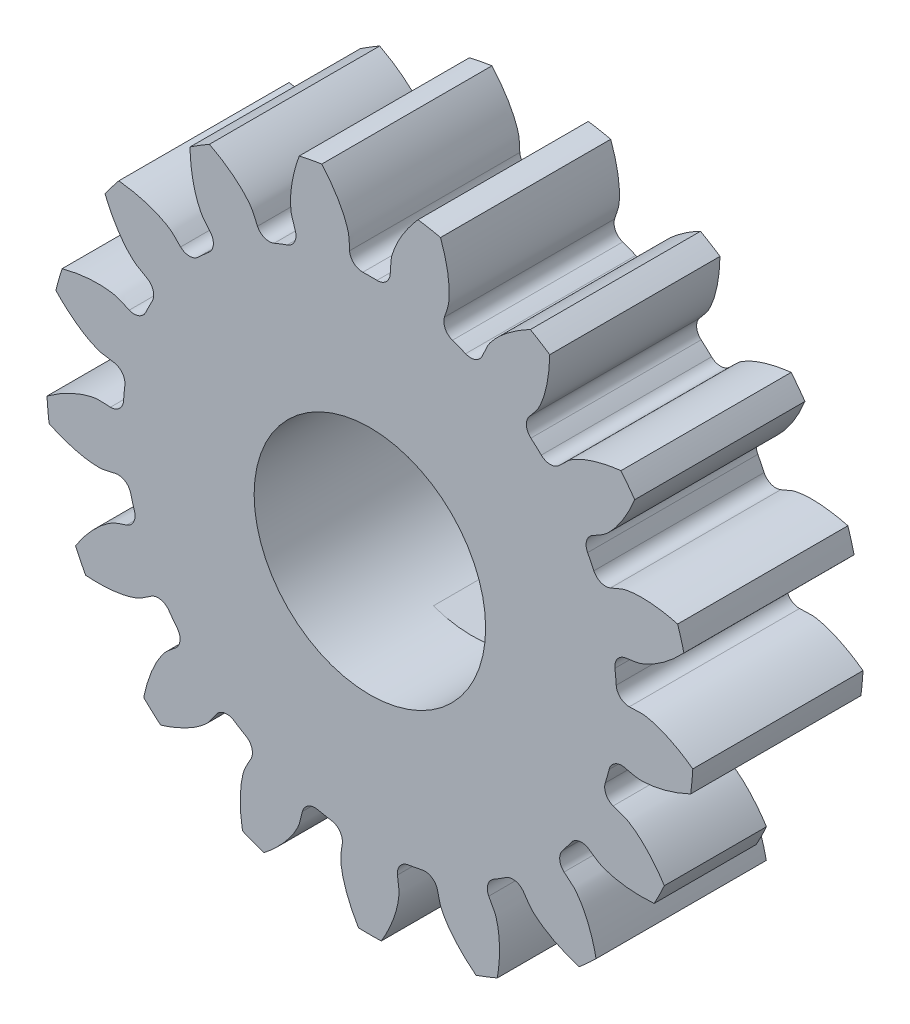
SolidWorks part; units mm, degrees
material "POM 乙缩醛共聚物"
ref_plane "前视基准面" through (0, 0, 0) normal (0, 0, 1) x (1, 0, 0)
ref_plane "上视基准面" through (0, 0, 0) normal (0, 1, 0) x (1, 0, 0)
ref_plane "右视基准面" through (0, 0, 0) normal (1, 0, 0) x (0, 0, -1)
ref_axis "Axis1" through (0, 0, -88.99) along (0, 0, 1)
sketch "草图1" plane through (0, 0, 0) normal (0, 0, 1) x (1, 0, 0)
  circle A0 centre (0, 0) radius 9.5
extrude "LaShenA" add sketch "草图1" along normal blind 5
sketch "SketchA" plane through (0, 0, 5) normal (0, 0, 1) x (1, 0, 0)
  line L0 (0, 0) -> (0, 9.5) construction
  arc A0 (0.207, 7.247) -> (-0.207, 7.247) centre (0, 0) ccw
  arc A1 (1.9284, 9.9057) -> (-1.9284, 9.9057) centre (0, 0) ccw
  arc A2 (-0.207, 7.247) -> (-0.5968, 7.5982) centre (-0.2179, 7.6269) cw
  arc A3 (0.5968, 7.5982) -> (0.207, 7.247) centre (0.2179, 7.6269) cw
  circle A4 centre (0, 0) radius 7.9874 construction
  circle A5 centre (0, 0) radius 9.5 construction
  circle A6 centre (0, 0) radius 7.25 construction
  circle A7 centre (0, 0) radius 8.5 construction
  spline S0 degree 3 poles (0.5968, 7.5982) (0.606, 7.7206) (0.6026, 7.8698) (0.6296, 8.029) (0.6422, 8.0808) (0.6533, 8.1218) (0.6675, 8.1687) (0.685, 8.2214) (0.7063, 8.2797) (0.7317, 8.3435) (0.7614, 8.4125) (0.7959, 8.4865) (0.8354, 8.5654) (0.8802, 8.6489) (0.9307, 8.7367) (0.987, 8.8286) (1.0495, 8.9244) (1.1185, 9.0236) (1.1941, 9.1262) (1.2767, 9.2316) (1.3664, 9.3397) (1.4635, 9.4501) (1.5682, 9.5624) (1.7212, 9.7175) (1.8433, 9.8309) (1.9284, 9.9057) knots 0.121184 0.121184 0.121184 0.121184 0.238206 0.264317 0.275812 0.289397 0.305072 0.322837 0.342692 0.364637 0.388672 0.414798 0.443013 0.473318 0.505713 0.540198 0.576773 0.615438 0.656194 0.699039 0.743974 0.790999 0.840114 0.89132 1 1 1 1
  spline S1 degree 3 poles (-0.5968, 7.5982) (-0.606, 7.7206) (-0.6026, 7.8698) (-0.6296, 8.029) (-0.6422, 8.0808) (-0.6533, 8.1218) (-0.6675, 8.1687) (-0.685, 8.2214) (-0.7063, 8.2797) (-0.7317, 8.3435) (-0.7614, 8.4125) (-0.7959, 8.4865) (-0.8354, 8.5654) (-0.8802, 8.6489) (-0.9307, 8.7367) (-0.987, 8.8286) (-1.0495, 8.9244) (-1.1185, 9.0236) (-1.1941, 9.1262) (-1.2767, 9.2316) (-1.3664, 9.3397) (-1.4635, 9.4501) (-1.5682, 9.5624) (-1.7212, 9.7175) (-1.8433, 9.8309) (-1.9284, 9.9057) knots 0.121184 0.121184 0.121184 0.121184 0.238206 0.264317 0.275812 0.289397 0.305072 0.322837 0.342692 0.364637 0.388672 0.414798 0.443013 0.473318 0.505713 0.540198 0.576773 0.615438 0.656194 0.699039 0.743974 0.790999 0.840114 0.89132 1 1 1 1
  dimension "D1" = 0.38
  dimension "Db" = 15.9748
  dimension "Da" = 19
  dimension "Df" = 14.5
  dimension "Dn" = 17
extrude "Cut-ExtrudeA" cut sketch "SketchA" against normal blind 30
pattern_circular "www.KYTool.cn" count 17 over 360 about axis through (0, 0, -88.99) along (0, 0, 1) of "Cut-ExtrudeA"
sketch "草图3" plane through (0, 0, 0) normal (0, 0, -1) x (-1, 0, 0)
  line L2 (-13.5943, -8.4259) -> (1.1359, -3.2046)
  line L3 (-1.7247, 2.9301) -> (-15.1929, -4.9977)
  line L4 (-13.5943, -8.4259) -> (1.1359, -3.2046)
  line L5 (-1.7247, 2.9301) -> (-15.1929, -4.9977)
  arc A2 (1.1359, -3.2046) -> (-1.7247, 2.9301) centre (0, 0) ccw
  arc A3 (-15.1929, -4.9977) -> (-13.5943, -8.4259) centre (-14.229, -6.6351) ccw
  arc A4 (1.1359, -3.2046) -> (-1.7247, 2.9301) centre (0, 0) ccw
  arc A5 (-15.1929, -4.9977) -> (-13.5943, -8.4259) centre (-14.229, -6.6351) ccw
  dimension "D1" = 0
extrude "切除-拉伸2" cut sketch "草图3" against normal up to surface (2 mm away)
sketch "草图4" plane through (0, 0, 2) normal (0, 0, -1) x (-1, 0, 0)
  circle A2 centre (0, 0) radius 3.4
extrude "切除-拉伸3" cut sketch "草图4" against normal through all
